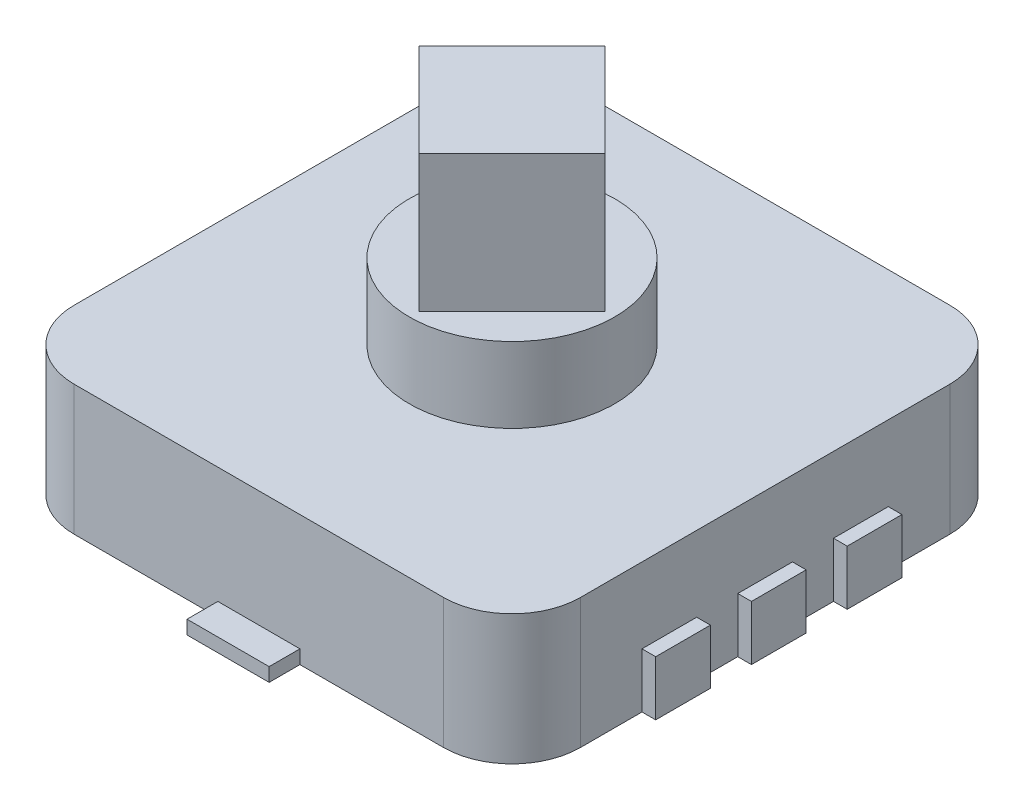
SolidWorks part; units mm, degrees
ref_plane "Płaszczyzna przednia" through (0, 0, 0) normal (0, 0, 1) x (1, 0, 0)
ref_plane "Płaszczyzna górna" through (0, 0, 0) normal (0, 1, 0) x (1, 0, 0)
ref_plane "Płaszczyzna prawa" through (0, 0, 0) normal (1, 0, 0) x (0, 0, -1)
sketch "Szkic2" plane through (0, 0, 0) normal (0, 1, 0) x (1, 0, 0)
  line L1 (-3.7, -3.7) -> (3.7, -3.7)
  line L2 (-3.7, -3.7) -> (-3.7, 3.7)
  line L3 (-3.7, 3.7) -> (3.7, 3.7)
  line L4 (3.7, -3.7) -> (3.7, 3.7)
  line L5 (-3.7, -3.7) -> (3.7, 3.7) construction
  line L6 (-3.7, 3.7) -> (3.7, -3.7) construction
  point P0 (0, 0)
  dimension "D1" = 7.4
  dimension "D2" = 7.4
extrude "Dodanie-wyciągnięcie1" add sketch "Szkic2" along normal blind 1.9
sketch "Szkic3" plane through (0, 1.9, 0) normal (0, 1, 0) x (1, 0, 0)
  line L0 (0, -1.3576) -> (1.3576, 0)
  line L1 (0, -1.3576) -> (-1.3576, 0)
  line L2 (1.3576, 0) -> (0, 1.3576)
  line L3 (-1.3576, 0) -> (0, 1.3576)
  line L4 (0, -1.3576) -> (0, 1.3576) construction
  line L5 (1.3576, 0) -> (-1.3576, 0) construction
  line L6 (-3.7, -3.7) -> (3.7, -3.7) construction
  point P1 (0, 0)
  dimension "D1" = 1.92
extrude "Dodanie-wyciągnięcie2" add sketch "Szkic3" along normal blind 5 from surface at -1.9 starting at face at (0, 0, 0)
sketch "Szkic4" plane through (0, 1.9, 0) normal (0, 1, 0) x (1, 0, 0)
  circle A0 centre (0, 0) radius 1.5
  dimension "D1" = 3
extrude "Dodanie-wyciągnięcie3" add sketch "Szkic4" along normal blind 3 from surface at -1.9 starting at face at (0, 0, 0)
sketch "Szkic5" plane through (0, 0, 0) normal (0, -1, 0) x (1, 0, 0)
  line L0 (-3.7, 0) -> (3.7, 0) construction
  line L1 (-3.7, -3.7) -> (-3.7, 3.7) construction
  line L2 (3.7, 3.7) -> (3.7, -3.7) construction
  circle A0 centre (0, 1.9) radius 0.45
  circle A1 centre (0, -1.9) radius 0.45
  point P9 (0, 0)
  dimension "D1" = 0.9
  dimension "D2" = 1.9
extrude "Dodanie-wyciągnięcie4" add sketch "Szkic5" along normal blind 0.5
sketch "Szkic6" plane through (3.7, 0, 0) normal (1, 0, 0) x (0, 0, -1)
  line L0 (-3.7, 0) -> (3.7, 0) construction
  line L1 (-1, 0) -> (-1.8, 0)
  line L2 (-1, 0) -> (-1, 0.8)
  line L3 (-1, 0.8) -> (-1.8, 0.8)
  line L4 (-1.8, 0) -> (-1.8, 0.8)
  line L5 (-1, 0) -> (-1.8, 0.8) construction
  line L6 (-1, 0.8) -> (-1.8, 0) construction
  line L7 (0.4, 0) -> (-0.4, 0)
  line L8 (0.4, 0) -> (0.4, 0.8)
  line L9 (0.4, 0.8) -> (-0.4, 0.8)
  line L10 (-0.4, 0) -> (-0.4, 0.8)
  line L11 (0.4, 0) -> (-0.4, 0.8) construction
  line L12 (0.4, 0.8) -> (-0.4, 0) construction
  line L13 (1.8, 0) -> (1, 0)
  line L14 (1.8, 0) -> (1.8, 0.8)
  line L15 (1.8, 0.8) -> (1, 0.8)
  line L16 (1, 0) -> (1, 0.8)
  line L17 (1.8, 0) -> (1, 0.8) construction
  line L18 (1.8, 0.8) -> (1, 0) construction
  point P0 (-1.4, 0.4)
  point P5 (0, 0.4)
  point P10 (1.4, 0.4)
  point P15 (0, 0)
  dimension "D1" = 1.4
  dimension "D2" = 1.4
  dimension "D3" = 0.8
extrude "Dodanie-wyciągnięcie5" add sketch "Szkic6" along normal blind 0.2
mirror "Lustro1" about plane through (0, 0, 0) normal (1, 0, 0) of "Dodanie-wyciągnięcie5"
fillet "Zaokrąglenie1" radius 1 4 edges at (-3.7, 0.95, -3.7) (-3.7, 0.95, 3.7) (3.7, 0.95, -3.7) (3.7, 0.95, 3.7)
sketch "Szkic7" plane through (0, 0, 0) normal (0, -1, 0) x (1, 0, 0)
  line L0 (-2.7, 3.7) -> (2.7, 3.7) construction
  line L1 (-0.6, 4.15) -> (0.6, 4.15)
  line L2 (-0.6, 4.15) -> (-0.6, 3.25)
  line L3 (-0.6, 3.25) -> (0.6, 3.25)
  line L4 (0.6, 4.15) -> (0.6, 3.25)
  line L5 (-0.6, 4.15) -> (0.6, 3.25) construction
  line L6 (-0.6, 3.25) -> (0.6, 4.15) construction
  line L7 (-3.9, 0) -> (3.9, 0) construction
  line L8 (-3.9, 0.4) -> (-3.9, -0.4) construction
  line L9 (3.9, 0.4) -> (3.9, -0.4) construction
  line L10 (-0.6, -3.25) -> (0.6, -4.15) construction
  line L11 (-0.6, -4.15) -> (0.6, -3.25) construction
  line L12 (0.6, -4.15) -> (0.6, -3.25)
  line L13 (-0.6, -3.25) -> (0.6, -3.25)
  line L14 (-0.6, -4.15) -> (-0.6, -3.25)
  line L15 (-0.6, -4.15) -> (0.6, -4.15)
  point P0 (0, 3.7)
  point P17 (0, -3.7)
  dimension "D1" = 3.25
  dimension "D2" = 1.2
extrude "Dodanie-wyciągnięcie6" add sketch "Szkic7" against normal blind 0.2
